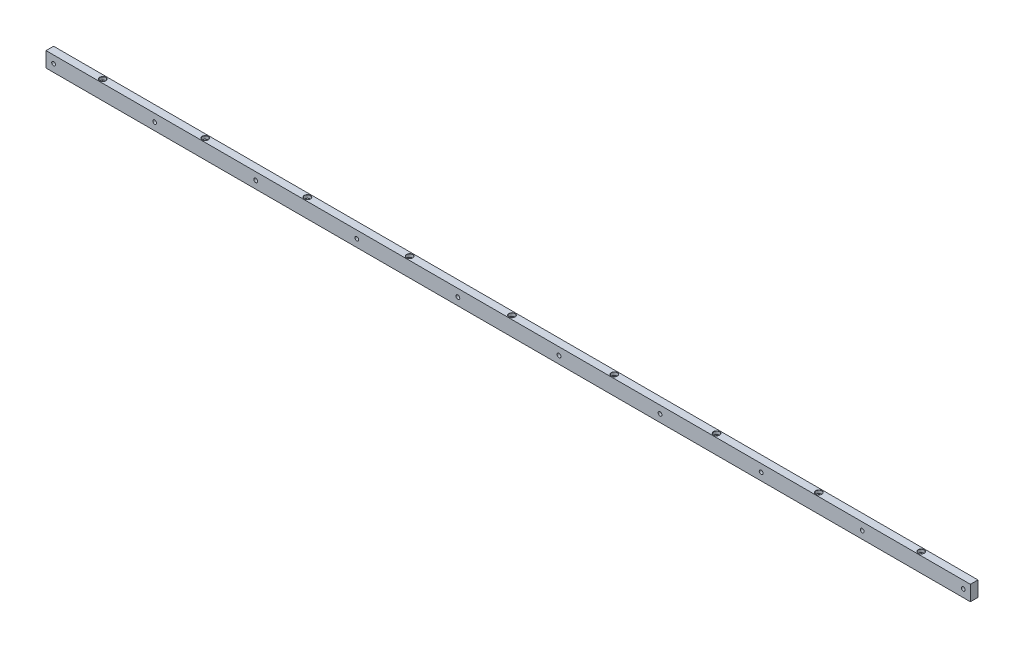
SolidWorks part; units mm, degrees
material "1060 Alloy"
ref_plane "Front Plane" through (0, 0, 0) normal (0, 0, 1) x (1, 0, 0)
ref_plane "Top Plane" through (0, 0, 0) normal (0, 1, 0) x (1, 0, 0)
ref_plane "Right Plane" through (0, 0, 0) normal (1, 0, 0) x (0, 0, -1)
sketch "Sketch1" plane through (0, 0, 0) normal (0, 0, 1) x (1, 0, 0)
  line L0 (0, 12.7) -> (1549.4, 12.7) construction
  line L1 (0, 0) -> (1549.4, 0)
  line L2 (0, 0) -> (0, 25.4)
  line L3 (0, 25.4) -> (1549.4, 25.4)
  line L4 (1549.4, 0) -> (1549.4, 25.4)
  circle A0 centre (12.7, 12.7) radius 3.175
  circle A1 centre (182.118, 12.7) radius 3.175
  circle A2 centre (351.536, 12.7) radius 3.175
  circle A3 centre (520.954, 12.7) radius 3.175
  circle A4 centre (690.372, 12.7) radius 3.175
  circle A5 centre (859.79, 12.7) radius 3.175
  circle A6 centre (1029.208, 12.7) radius 3.175
  circle A7 centre (1198.626, 12.7) radius 3.175
  circle A8 centre (1368.044, 12.7) radius 3.175
  circle A9 centre (1537.462, 12.7) radius 3.175
  dimension "D3" = 6.35
  dimension "D4" = 12.7
  dimension "D6" = 169.418
  dimension "D1" = 25.4
  dimension "D2" = 1549.4
  dimension "D5" = 10
extrude "Boss-Extrude1" add sketch "Sketch1" against normal blind 12.7
sketch "Sketch2" plane through (0, 25.4, 0) normal (0, 1, 0) x (1, 0, 0)
  line L0 (0, 6.35) -> (1549.4, 6.35) construction
  line L1 (0, 12.7) -> (0, 0) construction
  line L2 (1549.4, 12.7) -> (1549.4, 0) construction
  point P6 (88.9, 6.35)
  dimension "D1" = 88.9
hole_wizard "CBORE for #0 Binding Head Machine Screw1" positions "3DSketch1" profile "Sketch3" counterbore size "#0" standard "ANSI Inch" end condition through all
sketch3d "3DSketch1"
  point P0 (88.9, 25.4, -6.35)
sketch "Sketch3" plane through (88.9, 25.4, -6.35) normal (1, 0, 0) x (0, 0, 1)
  line L0 (0, 0) -> (0, 25.4)
  line L1 (0, 25.4) -> (2.7559, 25.4)
  line L3 (2.7559, 25.4) -> (2.7559, 5.08)
  line L4 (4.953, 5.08) -> (2.7559, 5.08)
  line L5 (4.953, 5.08) -> (4.953, 0.2413)
  line L6 (4.953, 0.2413) -> (5.1943, 0)
  line L7 (5.1943, 0) -> (0, 0)
  line L8 (-4.953, 0.2413) -> (-5.1943, 0) construction
  line L11 (0, -6.35) -> (0, 107.95) construction
  dimension "Thru Hole Dia." = 5.5118
  dimension "Thru Hole Depth" = 25.4
  dimension "C'Bore Dia." = 9.906
  dimension "C'Bore Depth" = 5.08
  dimension "Near C'Sink Dia." = 10.3886
  dimension "Near C'Sink Angle" = 90
pattern_linear "LPattern1" count 9 spacing 171.45 along (1, 0, 0) of "CBORE for #0 Binding Head Machine Screw1"
